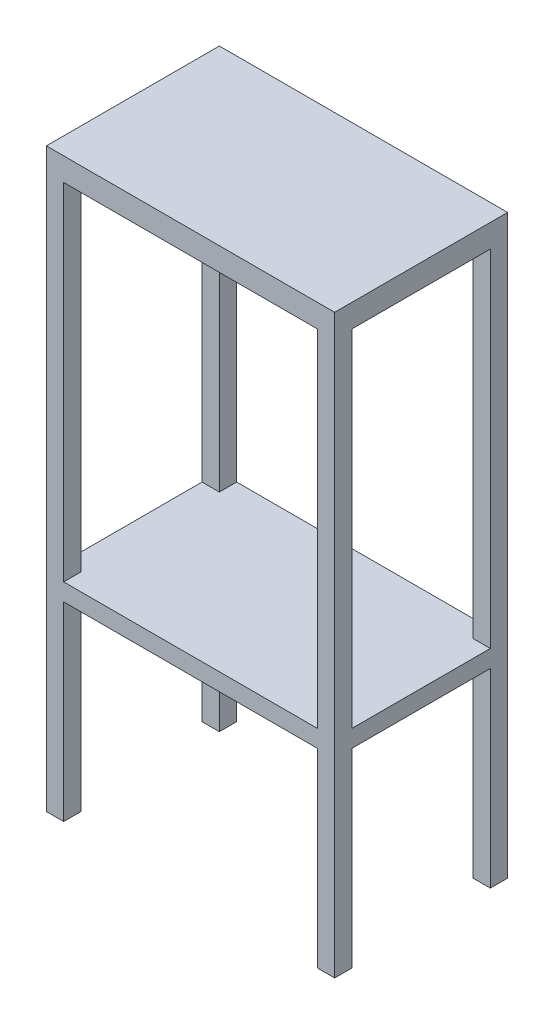
SolidWorks part; units mm, degrees
material "1023 Carbon Steel Sheet (SS)"
ref_plane "Front Plane" through (0, 0, 0) normal (0, 0, 1) x (1, 0, 0)
ref_plane "Top Plane" through (0, 0, 0) normal (0, 1, 0) x (1, 0, 0)
ref_plane "Right Plane" through (0, 0, 0) normal (1, 0, 0) x (0, 0, -1)
sketch "Sketch1" plane through (0, 0, 0) normal (0, 1, 0) x (1, 0, 0)
  line L1 (-250, 150) -> (250, 150)
  line L2 (-250, 150) -> (-250, -150)
  line L3 (-250, -150) -> (250, -150)
  line L4 (250, 150) -> (250, -150)
  line L5 (-250, 150) -> (250, -150) construction
  line L6 (-250, -150) -> (250, 150) construction
  point P0 (0, 0)
  dimension "D1" = 300
  dimension "D2" = 500
extrude "Boss-Extrude1" add sketch "Sketch1" along normal blind 1000
sketch "Sketch2" plane through (0, 0, 0) normal (0, 0, 1) x (1, 0, 0)
  line L3 (-220, 960) -> (-220, 360)
  line L4 (-220, 960) -> (220, 960)
  line L5 (-220, 360) -> (220, 360)
  line L6 (220, 960) -> (220, 360)
  dimension "D1" = 440
  dimension "D2" = 600
extrude "Cut-Extrude1" cut sketch "Sketch2" against normal blind 1000 and the other way blind 1000
sketch "Sketch3" plane through (0, 0, 0) normal (0, 0, 1) x (1, 0, 0)
  line L0 (-250, 0) -> (250, 0) construction
  line L5 (220, 330) -> (-220, 330)
  line L6 (220, 330) -> (220, 0)
  line L7 (220, 0) -> (-220, 0)
  line L8 (-220, 330) -> (-220, 0)
extrude "Cut-Extrude2" cut sketch "Sketch3" against normal blind 1000 and the other way blind 1000
sketch "Sketch4" plane through (0, 0, 0) normal (1, 0, 0) x (0, 0, -1)
  line L3 (-120, 960) -> (-120, 360)
  line L4 (-120, 960) -> (120, 960)
  line L5 (120, 960) -> (120, 360)
  line L6 (120, 360) -> (-120, 360)
  dimension "D4" = 240
  dimension "D5" = 600
extrude "Cut-Extrude3" cut sketch "Sketch4" against normal blind 1000 and the other way blind 1000
sketch "Sketch5" plane through (0, 0, 0) normal (1, 0, 0) x (0, 0, -1)
  line L0 (-150, 0) -> (150, 0) construction
  line L5 (120, 330) -> (-120, 330)
  line L6 (120, 330) -> (120, 0)
  line L7 (120, 0) -> (-120, 0)
  line L8 (-120, 330) -> (-120, 0)
extrude "Cut-Extrude4" cut sketch "Sketch5" against normal blind 1000 and the other way blind 1000
